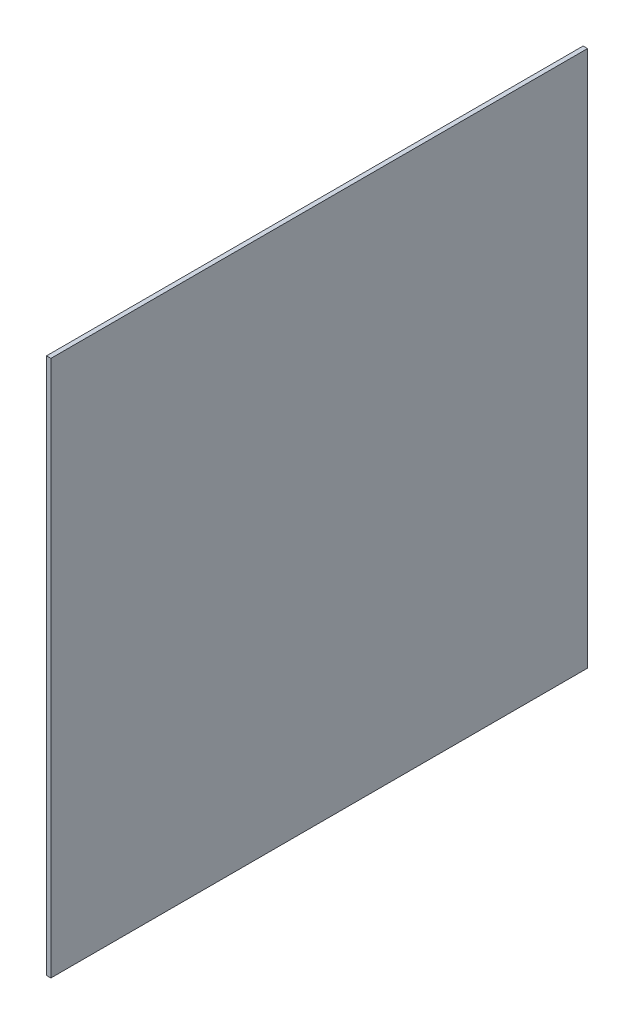
SolidWorks part; units mm, degrees
material "Glass"
ref_plane "Front Plane" through (0, 0, 0) normal (0, 0, 1) x (1, 0, 0)
ref_plane "Top Plane" through (0, 0, 0) normal (0, 1, 0) x (1, 0, 0)
ref_plane "Right Plane" through (0, 0, 0) normal (1, 0, 0) x (0, 0, -1)
sketch "Sketch1" plane through (0, 0, 0) normal (1, 0, 0) x (0, 0, -1)
  line L1 (-289.7188, -289.7188) -> (289.7187, -289.7188)
  line L2 (-289.7188, -289.7188) -> (-289.7188, 289.7187)
  line L3 (-289.7188, 289.7187) -> (289.7187, 289.7187)
  line L4 (289.7187, -289.7188) -> (289.7187, 289.7187)
  line L5 (-289.7188, -289.7188) -> (289.7187, 289.7187) construction
  line L6 (-289.7188, 289.7187) -> (289.7187, -289.7188) construction
  point P0 (0, 0)
  dimension "D1" = 579.4375
  dimension "D2" = 579.4375
extrude "Boss-Extrude1" add sketch "Sketch1" along normal blind 4.7625
